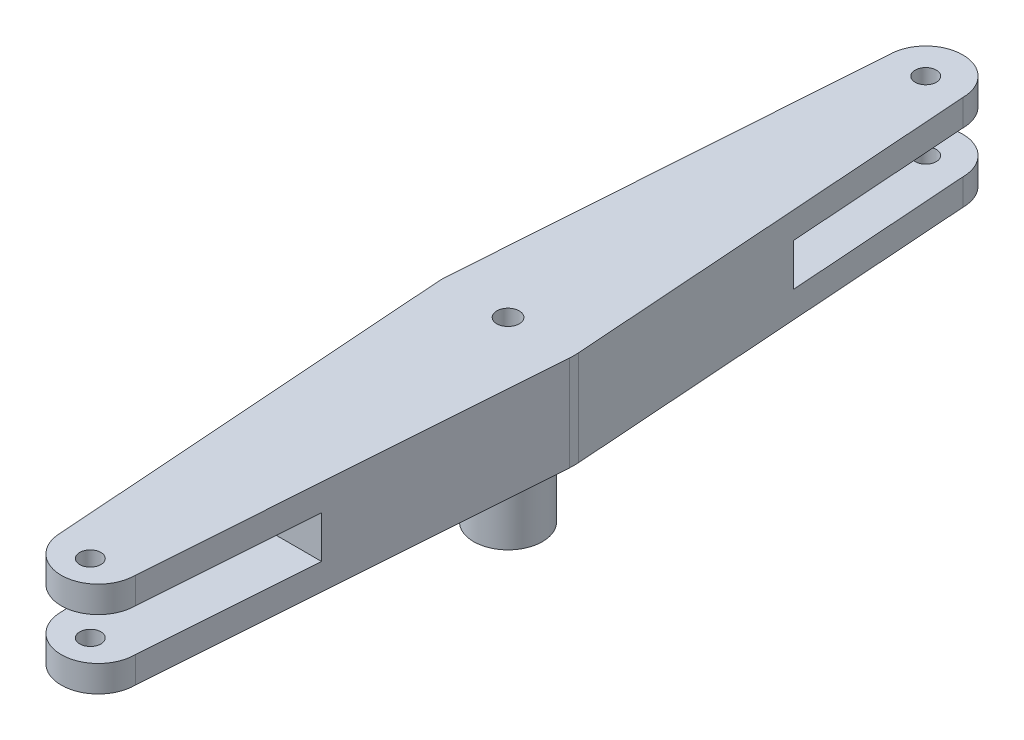
SolidWorks part; units mm, degrees
ref_plane "Front Plane" through (0, 0, 0) normal (0, 0, 1) x (1, 0, 0)
ref_plane "Top Plane" through (0, 0, 0) normal (0, 1, 0) x (1, 0, 0)
ref_plane "Right Plane" through (0, 0, 0) normal (1, 0, 0) x (0, 0, -1)
sketch "Sketch1" plane through (0, 0, 0) normal (0, 1, 0) x (1, 0, 0)
  line L0 (0, 0) -> (0, 79) construction
  line L1 (0, 0) -> (0, -77.5) construction
  line L2 (-7, 79) -> (-12.4695, 0.873)
  line L3 (-12.4683, -0.89) -> (-7, -77.5)
  line L4 (12.4695, 0.873) -> (7, 79)
  line L5 (12.4683, -0.89) -> (7, -77.5)
  line L7 (0, 0) -> (-12.5, 0) construction
  line L8 (-7.5767, -34.4096) -> (7.5767, -34.4096) construction
  arc A0 (-12.4695, 0.873) -> (-12.4683, -0.89) centre (0, 0) ccw
  arc A1 (7, 79) -> (-7, 79) centre (0, 79) ccw
  arc A2 (-7, -77.5) -> (7, -77.5) centre (0, -77.5) ccw
  circle A3 centre (0, 0) radius 2.125
  arc A6 (12.4683, -0.89) -> (12.4695, 0.873) centre (0, 0) ccw
  dimension "D1" = 79
  dimension "D3" = 25
  dimension "D4" = 7
  dimension "D5" = 7
  dimension "D6" = 4.25
  dimension "D2" = 77.5
extrude "Boss-Extrude1" add sketch "Sketch1" along normal blind 5
sketch "Sketch2" plane through (0, 5, 0) normal (0, 1, 0) x (1, 0, 0)
  line L0 (0, 0) -> (10.4356, 0) construction
  circle A0 centre (0, 79) radius 2
  circle A1 centre (0, -79) radius 2
  dimension "D1" = 4
extrude "Cut-Extrude1" cut sketch "Sketch2" against normal blind 10
sketch "Sketch5" plane through (0, 0, 0) normal (0, -1, 0) x (1, 0, 0)
  line L0 (-12.5, 0.0085) -> (12.5, 0.0085) construction
  circle A0 centre (0, 0) radius 6.5
  arc A1 (-12.4683, 0.89) -> (-12.4695, -0.873) centre (0, 0) ccw construction
  arc A2 (12.4695, -0.873) -> (12.4683, 0.89) centre (0, 0) ccw construction
  dimension "D1" = 13
extrude "Boss-Extrude2" add sketch "Sketch5" along normal blind 15.5
sketch "Sketch6" plane through (0, 5, 0) normal (0, 1, 0) x (1, 0, 0)
  line L2 (-12.5, 0) -> (12.5, 0) construction
  line L5 (-9.4069, 44.6192) -> (9.4069, 44.6192)
  line L6 (-9.347, -44.6192) -> (9.347, -44.6192)
  line L15 (-7, 79) -> (-12.4695, 0.873)
  line L16 (-12.4683, -0.89) -> (-7, -77.5)
  line L17 (7, -77.5) -> (12.4683, -0.89)
  line L18 (12.4695, 0.873) -> (7, 79)
  line L19 (-9.4069, 44.6192) -> (-12.4695, 0.873)
  line L20 (-12.4683, -0.89) -> (-9.347, -44.6192)
  line L21 (9.347, -44.6192) -> (12.4683, -0.89)
  line L22 (12.4695, 0.873) -> (9.4069, 44.6192)
  arc A6 (7, 79) -> (-7, 79) centre (0, 79) ccw
  arc A12 (-12.4695, 0.873) -> (-12.4683, -0.89) centre (0, 0) ccw
  arc A13 (-7, -77.5) -> (7, -77.5) centre (0, -77.5) ccw
  arc A14 (12.4683, -0.89) -> (12.4695, 0.873) centre (0, 0) ccw
  arc A16 (-12.4695, 0.873) -> (-12.4683, -0.89) centre (0, 0) ccw
  arc A18 (12.4683, -0.89) -> (12.4695, 0.873) centre (0, 0) ccw
  dimension "D1" = 0
extrude "Boss-Extrude3" add sketch "Sketch6" along normal blind 8
sketch "Sketch7" plane through (0, 0, 44.6192) normal (0, 0, 1) x (1, 0, 0)
  line L0 (-9.347, 9) -> (9.347, 9) construction
  line L3 (-9.347, 13) -> (-9.347, 5) construction
  line L4 (9.347, 13) -> (9.347, 5) construction
ref_plane "Plane1" through (0, 9, 0) normal (0, 1, 0) x (1, 0, 0)
mirror "Mirror1" about plane through (0, 9, 0) normal (0, 1, 0) of "Cut-Extrude1", "Boss-Extrude1"
sketch "Sketch8" plane through (0, -15.5, 0) normal (0, -1, 0) x (1, 0, 0)
  circle A0 centre (0, 0) radius 2
extrude "Cut-Extrude2" cut sketch "Sketch8" against normal through all
sketch "Sketch9" plane through (0, -15.5, 0) normal (0, -1, 0) x (1, 0, 0)
  circle A0 centre (0, 0) radius 6.125
  dimension "D1" = 12.25
